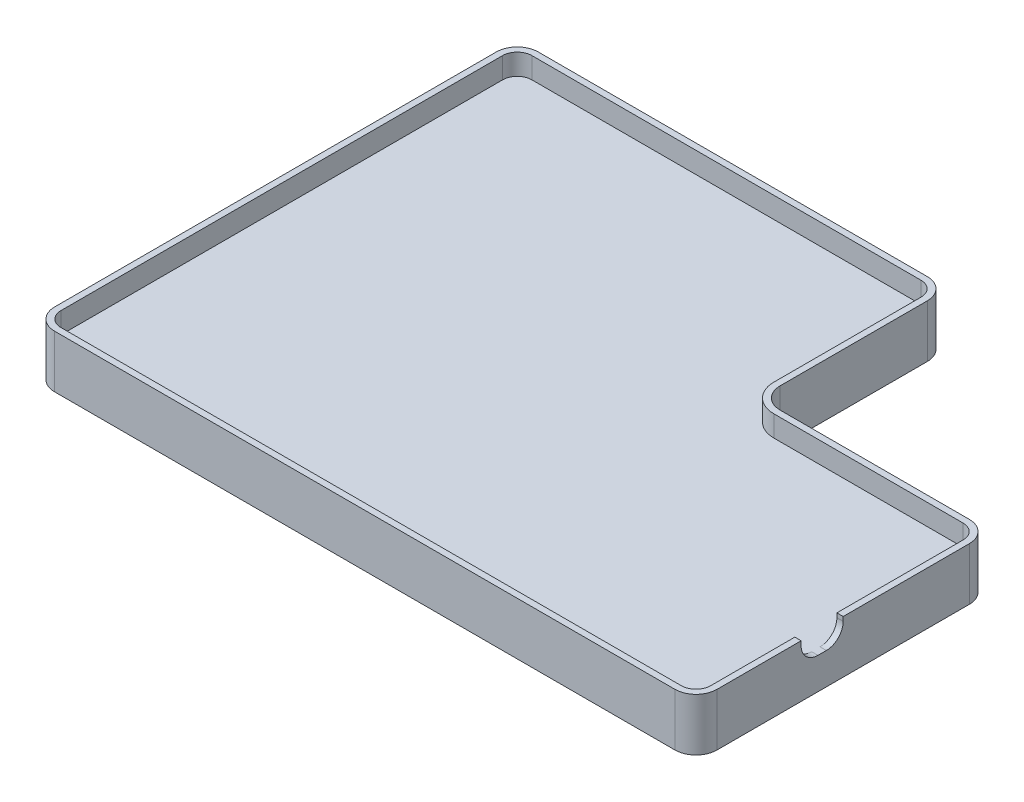
SolidWorks part; units mm, degrees
material "Chrome Stainless Steel"
ref_plane "Front Plane" through (0, 0, 0) normal (0, 0, 1) x (1, 0, 0)
ref_plane "Top Plane" through (0, 0, 0) normal (0, 1, 0) x (1, 0, 0)
ref_plane "Right Plane" through (0, 0, 0) normal (1, 0, 0) x (0, 0, -1)
sketch "Sketch1" plane through (0, 0, 0) normal (0, 1, 0) x (1, 0, 0)
  line L0 (305, 140) -> (215, 140)
  line L1 (10, 0) -> (305, 0)
  line L2 (0, 10) -> (0, 220)
  line L3 (10, 230) -> (195, 230)
  line L4 (315, 10) -> (315, 130)
  line L5 (205, 150) -> (205, 220)
  arc A0 (10, 0) -> (0, 10) centre (10, 10) cw
  arc A1 (305, 0) -> (315, 10) centre (305, 10) ccw
  arc A2 (305, 140) -> (315, 130) centre (305, 130) cw
  arc A3 (215, 140) -> (205, 150) centre (215, 150) cw
  arc A4 (205, 220) -> (195, 230) centre (195, 220) ccw
  arc A5 (0, 220) -> (10, 230) centre (10, 220) cw
  point P9 (0, 0)
  point P12 (315, 0)
  point P15 (315, 140)
  point P18 (205, 140)
  dimension "D2" = 10
  dimension "D1" = 315
  dimension "D3" = 90
  dimension "D4" = 110
  dimension "D5" = 230
extrude "Boss-Extrude1" add sketch "Sketch1" along normal blind 5
sketch "Sketch3" plane through (0, 0, 0) normal (0, 1, 0) x (1, 0, 0)
  line L24 (10, 3) -> (305, 3)
  line L25 (312, 10) -> (312, 130)
  line L26 (305, 137) -> (215, 137)
  line L27 (202, 150) -> (202, 220)
  line L28 (195, 227) -> (10, 227)
  line L29 (3, 220) -> (3, 10)
  line L30 (10, 3) -> (305, 3)
  line L31 (312, 10) -> (312, 130)
  line L32 (305, 137) -> (215, 137)
  line L33 (202, 150) -> (202, 220)
  line L34 (195, 227) -> (10, 227)
  line L35 (3, 220) -> (3, 10)
  line L36 (10, 0) -> (305, 0)
  line L37 (315, 10) -> (315, 130)
  line L38 (305, 140) -> (215, 140)
  line L39 (205, 150) -> (205, 220)
  line L40 (195, 230) -> (10, 230)
  line L41 (0, 220) -> (0, 10)
  line L42 (10, 0) -> (305, 0)
  line L43 (315, 10) -> (315, 130)
  line L44 (305, 140) -> (215, 140)
  line L45 (205, 150) -> (205, 220)
  line L46 (195, 230) -> (10, 230)
  line L47 (0, 220) -> (0, 10)
  arc A25 (305, 3) -> (312, 10) centre (305, 10) ccw
  arc A26 (312, 130) -> (305, 137) centre (305, 130) ccw
  arc A27 (202, 150) -> (215, 137) centre (215, 150) ccw
  arc A28 (202, 220) -> (195, 227) centre (195, 220) ccw
  arc A29 (10, 227) -> (3, 220) centre (10, 220) ccw
  arc A30 (3, 10) -> (10, 3) centre (10, 10) ccw
  arc A31 (305, 3) -> (312, 10) centre (305, 10) ccw
  arc A32 (312, 130) -> (305, 137) centre (305, 130) ccw
  arc A33 (202, 150) -> (215, 137) centre (215, 150) ccw
  arc A34 (202, 220) -> (195, 227) centre (195, 220) ccw
  arc A35 (10, 227) -> (3, 220) centre (10, 220) ccw
  arc A36 (3, 10) -> (10, 3) centre (10, 10) ccw
  arc A37 (305, 0) -> (315, 10) centre (305, 10) ccw
  arc A38 (315, 130) -> (305, 140) centre (305, 130) ccw
  arc A39 (205, 150) -> (215, 140) centre (215, 150) ccw
  arc A40 (205, 220) -> (195, 230) centre (195, 220) ccw
  arc A41 (10, 230) -> (0, 220) centre (10, 220) ccw
  arc A42 (0, 10) -> (10, 0) centre (10, 10) ccw
  arc A43 (305, 0) -> (315, 10) centre (305, 10) ccw
  arc A44 (315, 130) -> (305, 140) centre (305, 130) ccw
  arc A45 (205, 150) -> (215, 140) centre (215, 150) ccw
  arc A46 (205, 220) -> (195, 230) centre (195, 220) ccw
  arc A47 (10, 230) -> (0, 220) centre (10, 220) ccw
  arc A48 (0, 10) -> (10, 0) centre (10, 10) ccw
  dimension "D1" = 3
  dimension "D2" = 0
extrude "Boss-Extrude2" add sketch "Sketch3" along normal blind 15 and the other way blind 10
sketch "Sketch4" plane through (315, 0, 0) normal (1, 0, 0) x (0, 0, -1)
  line L0 (50, 15) -> (50, 13)
  line L1 (10, 15) -> (130, 15) construction
  line L2 (62, 5) -> (58, 5)
  line L3 (70, 13) -> (70, 15)
  line L4 (0, 15) -> (0, -10) construction
  line L5 (70, 15) -> (50, 15)
  arc A0 (50, 13) -> (58, 5) centre (58, 13) ccw
  arc A1 (70, 13) -> (62, 5) centre (62, 13) cw
  point P10 (50, 5)
  point P14 (70, 5)
  dimension "D3" = 10
  dimension "D5" = 8
  dimension "D1" = 50
  dimension "D2" = 20
  dimension "D4" = 10
extrude "Cut-Extrude1" cut sketch "Sketch4" against normal blind 10
fillet "Fillet1" radius 5 12 edges at (309.9497, 0, -5.0503) (312, 0, -70) (309.9497, 0, -134.9497) (260, 0, -137) (205.8076, 0, -140.8076) (202, 0, -185) (199.9497, 0, -224.9497) (102.5, 0, -227) (5.0503, 0, -224.9497) (3, 0, -115) (5.0503, 0, -5.0503) (157.5, 0, -3)
